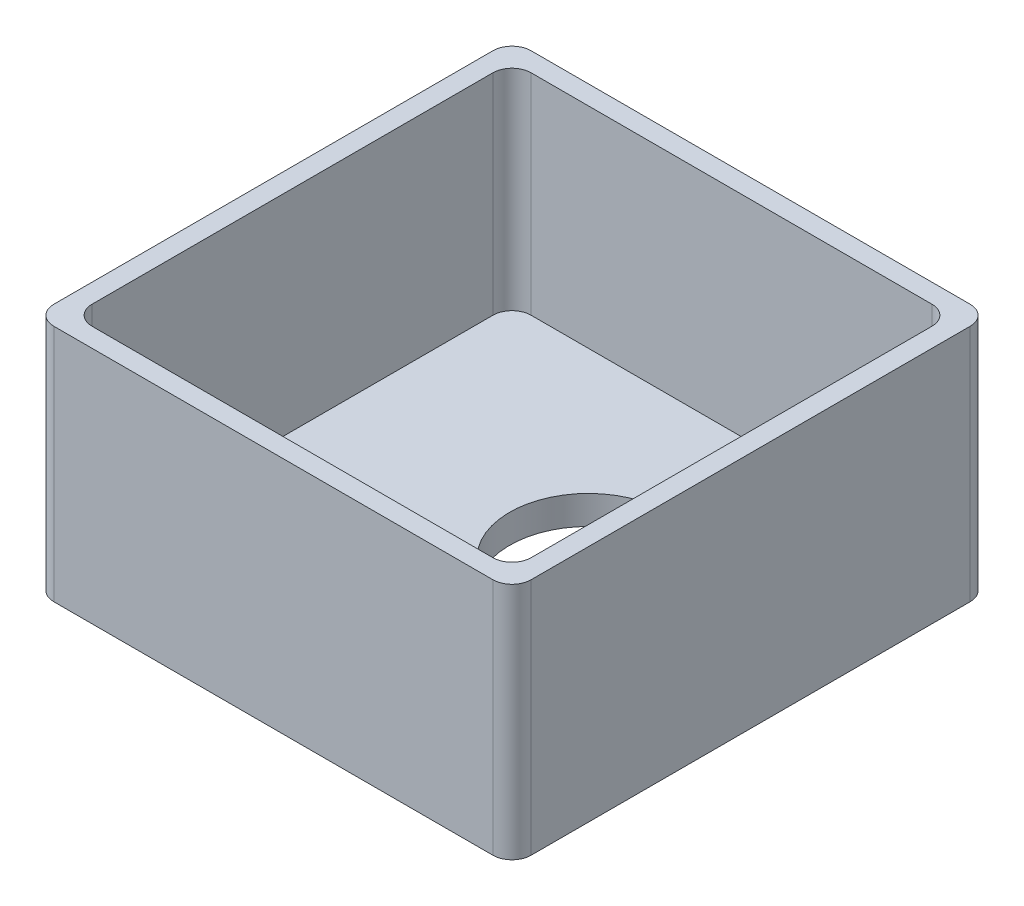
SolidWorks part; units mm, degrees
ref_plane "Płaszczyzna przednia" through (0, 0, 0) normal (0, 0, 1) x (1, 0, 0)
ref_plane "Płaszczyzna górna" through (0, 0, 0) normal (0, 1, 0) x (1, 0, 0)
ref_plane "Płaszczyzna prawa" through (0, 0, 0) normal (1, 0, 0) x (0, 0, -1)
sketch "Szkic3" plane through (0, 0, 0) normal (0, 1, 0) x (1, 0, 0)
  line L1 (-25, -25) -> (25, -25)
  line L2 (-25, -25) -> (-25, 25)
  line L3 (-25, 25) -> (25, 25)
  line L4 (25, -25) -> (25, 25)
  line L5 (-25, -25) -> (25, 25) construction
  line L6 (-25, 25) -> (25, -25) construction
  circle A0 centre (4, 4) radius 18
  circle A1 centre (4, 4) radius 8.25
  point P0 (0, 0)
  dimension "D3" = 36
  dimension "D4" = 21
  dimension "D5" = 16.5
  dimension "D1" = 50
  dimension "D2" = 50
extrude "Dodanie-wyciągnięcie2" add sketch "Szkic3" along normal blind 3 contours L1 L4 L3 L2 A0 | A0 A1
sketch "Szkic4" plane through (0, 3, 0) normal (0, 1, 0) x (1, 0, 0)
  line L1 (-25, -25) -> (25, -25)
  line L2 (-25, -25) -> (-25, 25)
  line L3 (-25, 25) -> (25, 25)
  line L4 (25, -25) -> (25, 25)
  line L5 (-25, -25) -> (25, 25) construction
  line L6 (-25, 25) -> (25, -25) construction
  line L7 (-23, -23) -> (23, -23)
  line L8 (-23, -23) -> (-23, 23)
  line L9 (-23, 23) -> (23, 23)
  line L10 (23, -23) -> (23, 23)
  line L11 (-23, -23) -> (23, 23) construction
  line L12 (-23, 23) -> (23, -23) construction
  point P0 (0, 0)
  point P5 (0, 0)
  dimension "D1" = 2
extrude "Dodanie-wyciągnięcie3" add sketch "Szkic4" along normal blind 22
fillet "Zaokrąglenie1" radius 2 8 edges at (-25, 12.5, 25) (-23, 14, 23) (25, 12.5, 25) (23, 14, 23) (25, 12.5, -25) (23, 14, -23) (-25, 12.5, -25) (-23, 14, -23)
